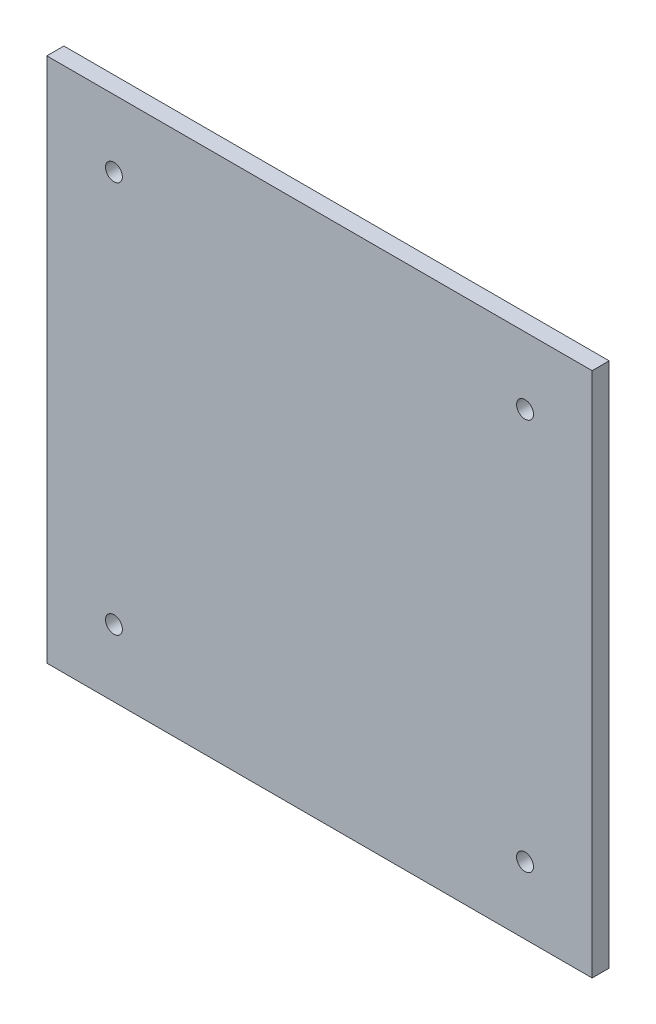
SolidWorks part; units mm, degrees
ref_plane "Top Plane" through (0, 0, 0) normal (0, 0, 1) x (1, 0, 0)
ref_plane "Front Plane" through (0, 0, 0) normal (0, 1, 0) x (1, 0, 0)
ref_plane "Right Plane" through (0, 0, 0) normal (1, 0, 0) x (0, 0, -1)
sketch "Profile Sketch" plane through (0, 0, 0) normal (0, 0, 1) x (1, 0, 0)
  line L1 (-50.8, -49) -> (50.8, -49)
  line L2 (-50.8, -49) -> (-50.8, 49)
  line L3 (-50.8, 49) -> (50.8, 49)
  line L4 (50.8, -49) -> (50.8, 49)
  line L5 (-50.8, -49) -> (50.8, 49) construction
  line L6 (-50.8, 49) -> (50.8, -49) construction
  point P0 (0, 0)
  dimension "D1" = 98
  dimension "D2" = 101.6
extrude "Profile Extrude" add sketch "Profile Sketch" along normal blind 3.175
sketch "Mounting Hole Sketch" plane through (0, 0, 3.175) normal (0, 0, 1) x (1, 0, 0)
  line L0 (50.8, 49) -> (-50.8, 49) construction
  line L1 (0, 0) -> (0, 49) construction
  line L2 (0, 0) -> (-50.8, 0) construction
  line L3 (-50.8, 49) -> (-50.8, -49) construction
  circle A0 centre (-38.3, 36.5) radius 1.575
  circle A1 centre (38.3, 36.5) radius 1.575
  circle A2 centre (38.3, -36.5) radius 1.575
  circle A3 centre (-38.3, -36.5) radius 1.575
  dimension "D1" = 3.15
  dimension "D2" = 12.5
  dimension "D3" = 12.5
extrude "Mounting Hole Cut" cut sketch "Mounting Hole Sketch" against normal through all
equation "\"D3@Mounting Hole Sketch\"=\"D2@Mounting Hole Sketch\""
